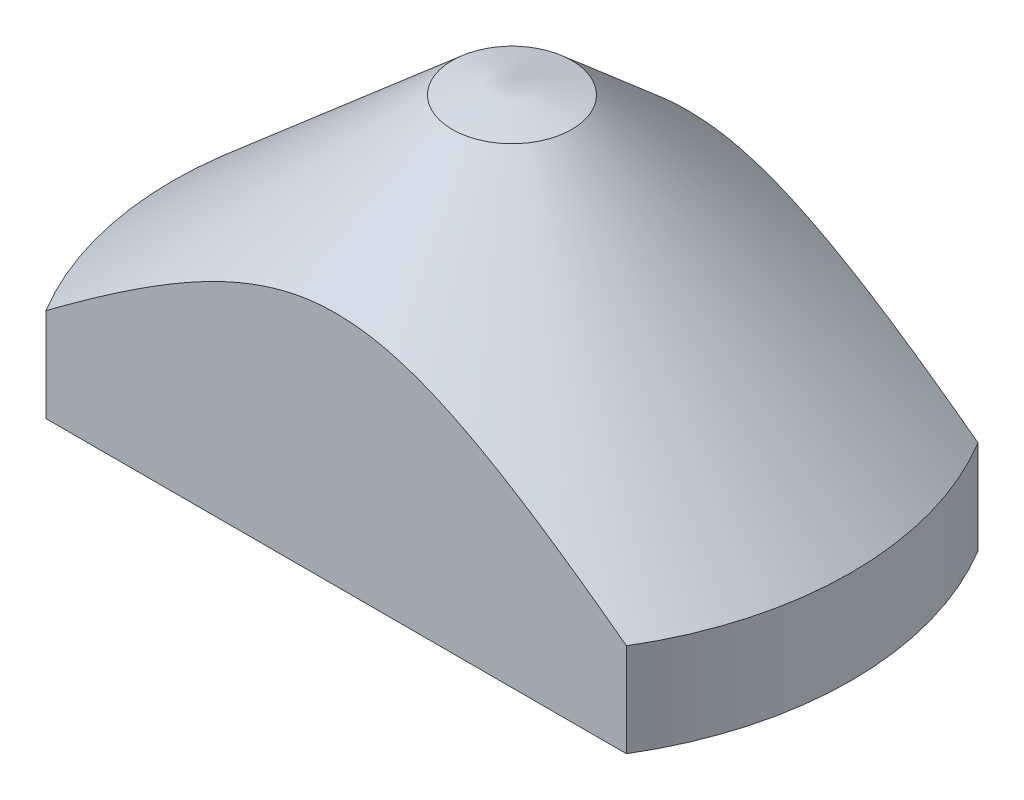
SolidWorks part; units mm, degrees
ref_plane "Alzado" through (0, 0, 0) normal (0, 0, 1) x (1, 0, 0)
ref_plane "Planta" through (0, 0, 0) normal (0, 1, 0) x (1, 0, 0)
ref_plane "Vista lateral" through (0, 0, 0) normal (1, 0, 0) x (0, 0, -1)
sketch "Croquis1" plane through (0, 0, 0) normal (0, 0, 1) x (1, 0, 0)
  line L0 (0, 53.5034) -> (0, -9.8601) construction
  line L1 (0, 0) -> (-48.25, 0)
  line L2 (-48.25, 0) -> (-48.25, 13.3)
  line L3 (-48.25, 13.3) -> (-8.5, 48)
  line L4 (-8.5, 48) -> (0, 50)
  line L5 (0, 0) -> (0, 50)
  point P5 (0, 53.5034)
  point P9 (0, 0)
  point P10 (0, 0)
  point P11 (0, 0)
  point P12 (-48.25, 17.3)
  point P13 (-39.3597, 48)
  point P14 (-20.6093, 48)
  dimension "D1" = 96.5
  dimension "D2" = 50
  dimension "D3" = 13.3
  dimension "D4" = 2
  dimension "D5" = 17
revolve "Revolución1" add sketch "Croquis1" angle 360 about L0
sketch "Croquis2" plane through (0, 0, 0) normal (0, -1, 0) x (1, 0, 0)
  line L1 (-41.2682, -25) -> (41.2682, -25)
  line L3 (-41.2682, 25) -> (41.2682, 25)
  line L5 (-41.2682, -25) -> (41.2682, 25) construction
  line L6 (-41.2682, 25) -> (41.2682, -25) construction
  circle A0 centre (0, 0) radius 48.25 construction
  arc A1 (-41.2682, 25) -> (-41.2682, -25) centre (0, 0) ccw
  arc A2 (41.2682, -25) -> (41.2682, 25) centre (0, 0) ccw
  point P0 (0, 0)
  circle M5 centre (0, 0) radius 48.25
  dimension "D1" = 50
extrude "Cortar-Extruir1" cut sketch "Croquis2" against normal through all contours L3 M5 | L1 M5
